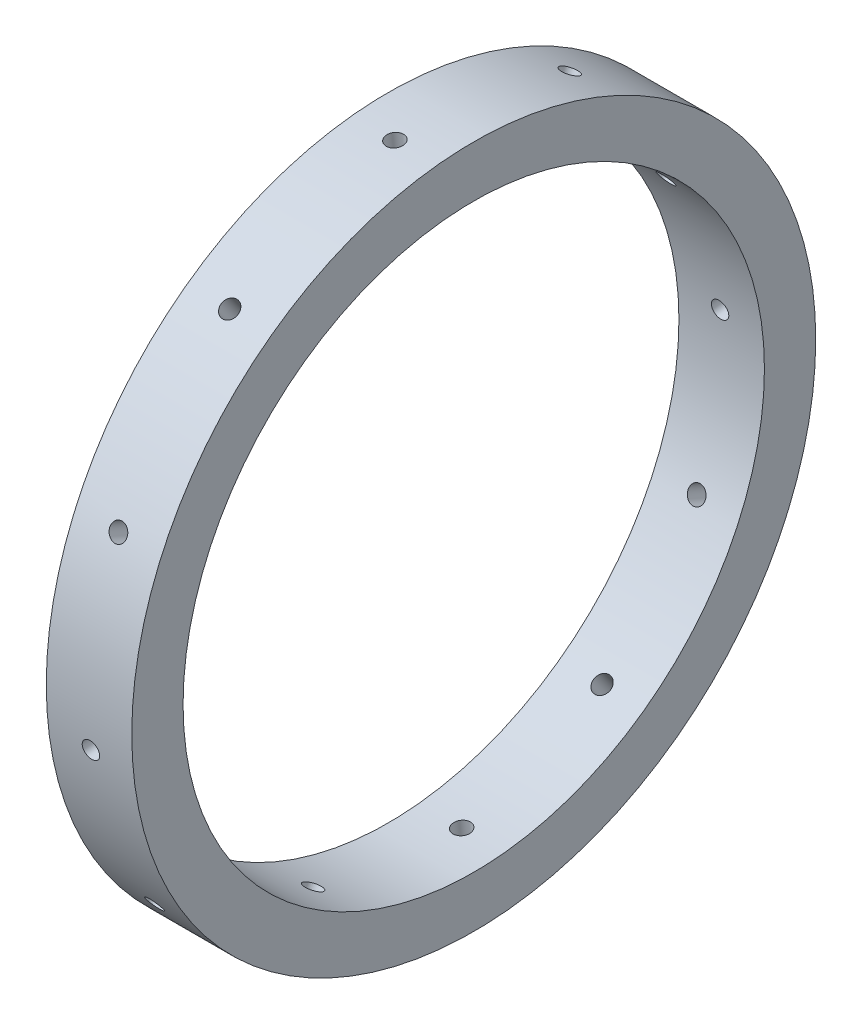
SolidWorks part; units mm, degrees
material "Nylon 101"
ref_plane "Front Plane" through (0, 0, 0) normal (0, 0, 1) x (1, 0, 0)
ref_plane "Top Plane" through (0, 0, 0) normal (0, 1, 0) x (1, 0, 0)
ref_plane "Right Plane" through (0, 0, 0) normal (1, 0, 0) x (0, 0, -1)
sketch "Sketch1" plane through (0, 0, 0) normal (1, 0, 0) x (0, 0, -1)
  circle A0 centre (0, 0) radius 43.18
  circle A1 centre (0, 0) radius 50.8
  dimension "D1" = 86.36
  dimension "D2" = 101.6
extrude "Boss-Extrude1" add sketch "Sketch1" along normal mid plane 12.7
sketch "Sketch2" plane through (0, 0, 0) normal (1, 0, 0) x (0, 0, -1)
  circle A0 centre (0, 0) radius 50.8
  circle A1 centre (0, 0) radius 50.8 construction
hole_wizard "#38 (0.1015) Diameter Hole1" positions "3DSketch3" profile "Sketch4" hole size "#38" standard "ANSI Inch"
sketch3d "3DSketch3"
  circle A0 centre (0, 0, 0) radius 50.8 construction
  point P0 (0, 50.5159, 5.3649)
  point P4 (50.8, 0, 0)
sketch "Sketch4" plane through (0, 50.5159, 5.3649) normal (1, 0, 0) x (0, -0.1056, 0.9944)
  line L0 (0, 0) -> (0, 111.1256)
  line L1 (0, 111.1256) -> (1.289, 111.1256)
  line L2 (1.289, 111.1256) -> (1.289, 0)
  line L5 (1.289, 0) -> (0, 0)
  line L11 (0, -6.35) -> (0, 107.95) construction
  dimension "Thru Hole Dia." = 2.5781
  dimension "Thru Hole Depth" = 111.1256
pattern_circular "CirPattern1" count 12 over 360 about axis through (6.35, 0, 0) along (-1, 0, 0) of "#38 (0.1015) Diameter Hole1"
